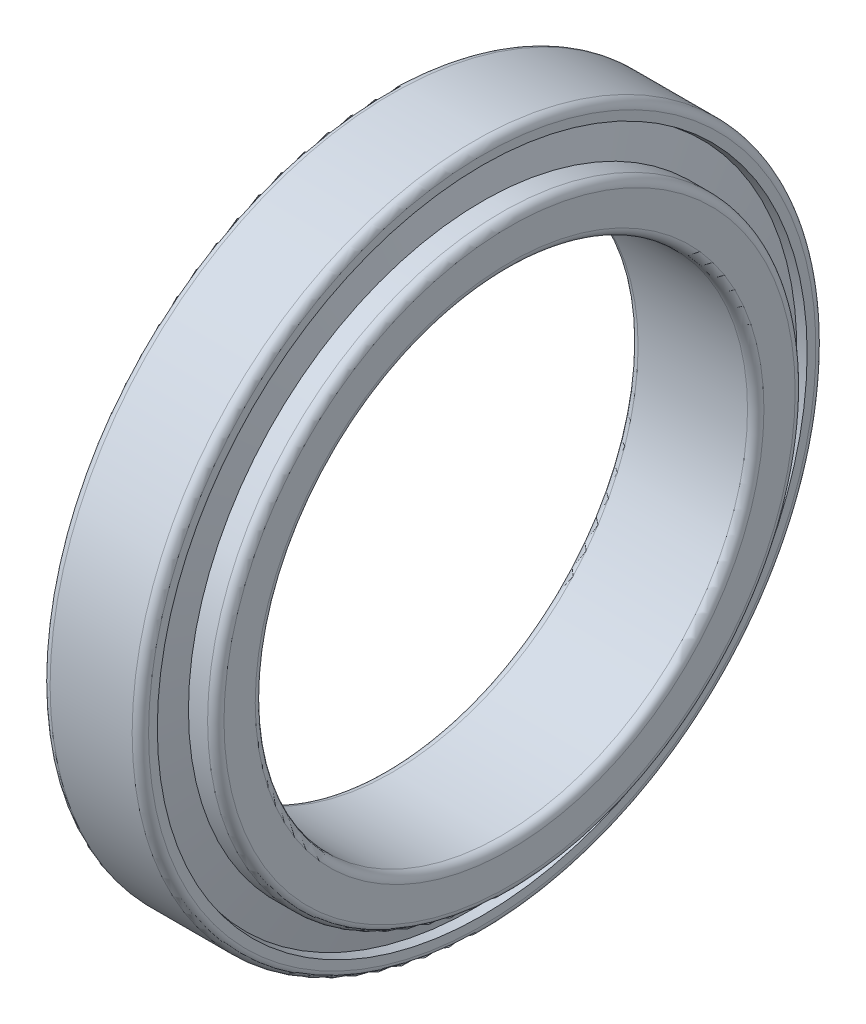
SolidWorks part; units mm, degrees
material "AISI Тип A2 Инструментальная сталь"
ref_plane "Спереди" through (0, 0, 0) normal (0, 0, 1) x (1, 0, 0)
ref_plane "Сверху" through (0, 0, 0) normal (0, 1, 0) x (1, 0, 0)
ref_plane "Справа" through (0, 0, 0) normal (1, 0, 0) x (0, 0, -1)
sketch "Эскиз1" plane through (0, 0, 0) normal (0, 0, 1) x (1, 0, 0)
  line L20 (-882.5277, 0) -> (43243.8573, 0) construction
  line L33 (1.6891, 55.9938) -> (0, 55.641)
  line L34 (0, 55.641) -> (0, 61)
  line L35 (1.5, 62.5) -> (16.5, 62.5)
  line L36 (18, 61) -> (18, 59.4003)
  line L37 (18, 59.4003) -> (16.4341, 59.0733)
  line L38 (1.6891, 55.9938) -> (16.4341, 59.0733) construction
  line L39 (3.3781, 48.5893) -> (0, 48.5893)
  line L40 (0, 48.5893) -> (0, 46.5)
  line L41 (1.5, 45) -> (21.5, 45)
  line L42 (23, 46.5) -> (23, 52.2087)
  line L43 (21.5, 53.7087) -> (18, 53.7087)
  line L44 (18, 53.7087) -> (18, 52.2087)
  line L45 (3.3781, 48.5893) -> (18, 52.2087) construction
  line L46 (18, 52.2087) -> (16.4341, 59.0733)
  line L47 (3.3781, 48.5893) -> (1.6891, 55.9938)
  line L48 (2.5336, 52.2915) -> (17.2171, 55.641) construction
  line L49 (0, 55.641) -> (17.2171, 55.641) construction
  line L50 (1.6891, 55.9938) -> (1.6891, 48.5893) construction
  arc A0 (0, 61) -> (1.5, 62.5) centre (1.5, 61) cw
  arc A1 (16.5, 62.5) -> (18, 61) centre (16.5, 61) cw
  arc A2 (0, 46.5) -> (1.5, 45) centre (1.5, 46.5) ccw
  arc A3 (23, 46.5) -> (21.5, 45) centre (21.5, 46.5) cw
  arc A4 (21.5, 53.7087) -> (23, 52.2087) centre (21.5, 52.2087) cw
  point P12 (17.2171, 55.641)
  dimension "гост r1" = 1.5
  dimension "гост r2" = 1.5
  dimension "гост DD" = 125
  dimension "гост B" = 23
  dimension "гост C" = 18
  dimension "гост T" = 23
  dimension "гост E" = 111.282
  dimension "гост d" = 90
  dimension "гост alfa" = 12.85
revolve "Повернуть1" add sketch "Эскиз1" angle 360 about L20
